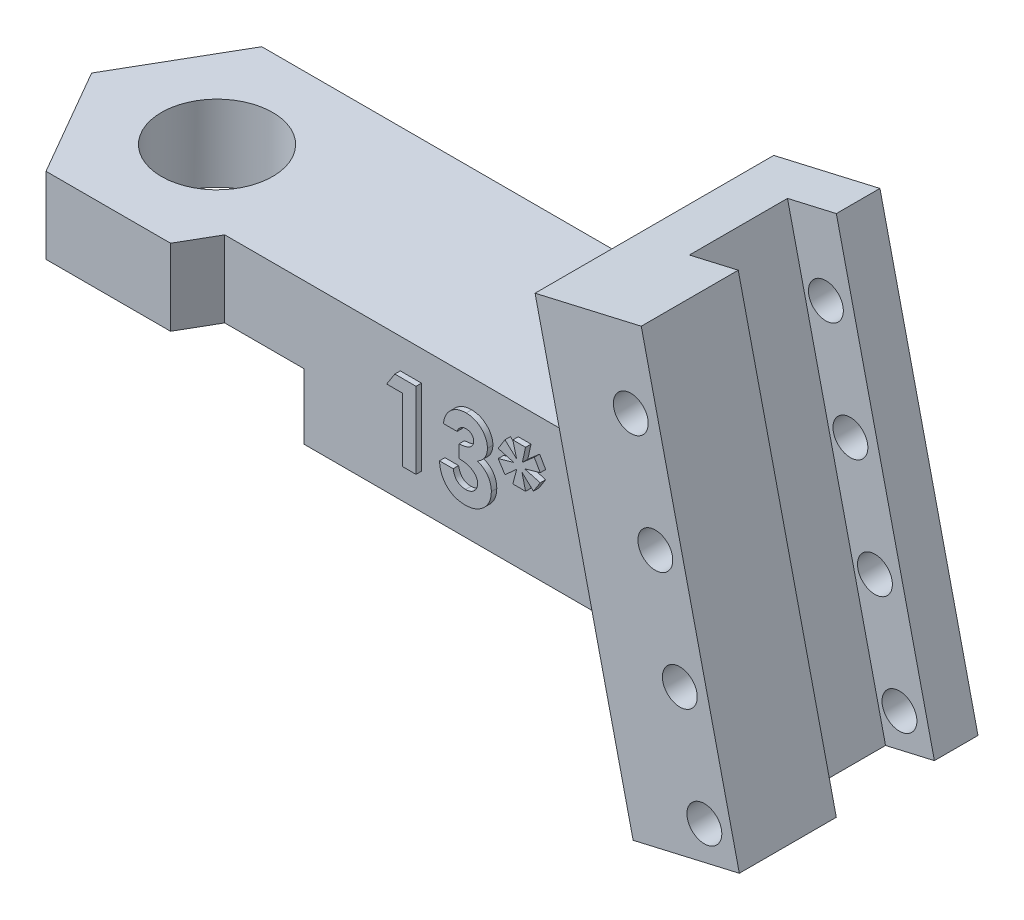
SolidWorks part; units mm, degrees
ref_plane "Front Plane" through (0, 0, 0) normal (0, 0, 1) x (1, 0, 0)
ref_plane "Top Plane" through (0, 0, 0) normal (0, 1, 0) x (1, 0, 0)
ref_plane "Right Plane" through (0, 0, 0) normal (1, 0, 0) x (0, 0, -1)
sketch "Sketch1" plane through (0, 0, 0) normal (0, 1, 0) x (1, 0, 0)
  line L1 (0, 0) -> (25, 0)
  line L2 (0, 0) -> (0, -6.75)
  line L3 (0, -6.75) -> (25, -6.75)
  line L4 (25, 0) -> (25, -6.75)
  dimension "D1" = 6.75
  dimension "D2" = 25
extrude "Boss-Extrude1" add sketch "Sketch1" along normal blind 6.5
ref_plane "Plane1" through (0, 0, 3.375) normal (0, 0, 1) x (1, 0, 0)
sketch "Sketch5" plane through (0, 6.5, 0) normal (0, 1, 0) x (1, 0, 0)
  line L0 (0, 0) -> (0, -6.75) construction
  line L1 (-5.7158, -3.375) -> (-2.8579, -8.325)
  line L2 (-2.8579, -8.325) -> (2.8579, -8.325)
  line L3 (2.8579, -8.325) -> (5.7158, -3.375)
  line L4 (5.7158, -3.375) -> (2.8579, 1.575)
  line L5 (2.8579, 1.575) -> (-2.8579, 1.575)
  line L6 (-2.8579, 1.575) -> (-5.7158, -3.375)
  circle A0 centre (0, -3.375) radius 4.95 construction
  dimension "D1" = 4.95
extrude "Boss-Extrude4" add sketch "Sketch5" against normal up to surface (6.5 mm away) up to face at (12.5, 0, 3.375)
sketch "Sketch3" plane through (0, 0, 3.375) normal (0, 0, 1) x (1, 0, 0)
  line L0 (20.6291, 13.925) -> (25.501, 15.0498)
  line L1 (25.501, 15.0498) -> (30, -4.4376)
  line L2 (30, -4.4376) -> (25.1281, -5.5624)
  line L3 (25.1281, -5.5624) -> (20.6291, 13.925)
  line L4 (3.7672, 6.5) -> (25, 6.5) construction
  point P6 (27.5641, -5)
  dimension "D1" = 30
  dimension "D2" = 5
  dimension "D3" = 20
  dimension "D4" = 77
  dimension "D6" = 5
extrude "Boss-Extrude3" add sketch "Sketch3" against normal up to surface (4.95 mm away) and the other way blind 6 up to face at (0, 3.25, -1.575)
sketch "Sketch4" plane through (-2.0083, 8.6988, 0) normal (-0.225, 0.9744, 0) x (0.9744, 0.225, 0)
  line L0 (28.2329, -9.375) -> (28.2329, 1.575) construction
  line L1 (25.9329, -0.425) -> (28.2329, -0.425)
  line L2 (25.9329, -0.425) -> (25.9329, -4.925)
  line L3 (25.9329, -4.925) -> (28.2329, -4.925)
  line L4 (28.2329, -0.425) -> (28.2329, -4.925)
  line L6 (28.2329, 1.575) -> (23.2329, 1.575) construction
  dimension "D1" = 4.5
  dimension "D2" = 2.3
  dimension "D3" = 2
extrude "Cut-Extrude1" cut sketch "Sketch4" against normal blind 23 contours L2 L3 L4 L1
sketch "Sketch6" plane through (0, 6.5, 0) normal (0, 1, 0) x (1, 0, 0)
  circle A0 centre (0, -3.3356) radius 2.55
  dimension "D1" = 5.1
extrude "Cut-Extrude2" cut sketch "Sketch6" against normal blind 10
sketch "Sketch7" plane through (0, 0, -1.575) normal (0, 0, -1) x (-1, 0, 0)
  line L0 (-2.8579, 0) -> (-23.844, 0)
  line L1 (-23.844, 0) -> (-25.1281, -5.5624)
  line L2 (-25.1281, -5.5624) -> (-30, -4.4376)
  line L3 (-30, -4.4376) -> (-25.501, 15.0498)
  line L4 (-25.501, 15.0498) -> (-20.6291, 13.925)
  line L5 (-20.6291, 13.925) -> (-22.3433, 6.5)
  line L6 (-22.3433, 6.5) -> (-2.8579, 6.5)
  line L7 (-2.8579, 6.5) -> (-2.8579, 0)
  dimension "D1" = 20
extrude "Boss-Extrude5" add sketch "Sketch7" against normal up to surface (1.575 mm away) up to face at (13.4304, 3.25, 0)
sketch "Sketch8" plane through (0, 0, 0) normal (0, -1, 0) x (-1, 0, 0)
  line L1 (-4.6765, -11.475) -> (4.6765, -11.475)
  line L2 (4.6765, -11.475) -> (9.3531, -3.375)
  line L3 (9.3531, -3.375) -> (4.6765, 4.725)
  line L4 (4.6765, 4.725) -> (-4.6765, 4.725)
  line L5 (-4.6765, 4.725) -> (-9.3531, -3.375)
  line L6 (-9.3531, -3.375) -> (-4.6765, -11.475)
  circle A0 centre (0, -3.375) radius 8.1 construction
  dimension "D1" = 16.2
extrude "Cut-Extrude3" cut sketch "Sketch8" against normal blind 3
sketch "Sketch9" plane through (0, 0, -1.575) normal (0, 0, -1) x (-1, 0, 0)
  line L0 (-30, -4.4376) -> (-25.501, 15.0498) construction
  line L1 (-25.1281, -5.5624) -> (-30, -4.4376) construction
  line L2 (-28.3959, -3.2685) -> (-25.0216, 11.347) construction
  line L3 (-30, -4.4376) -> (-25.501, 15.0498) construction
  circle A0 centre (-28.3959, -3.2685) radius 0.8
  circle A4 centre (-27.2711, 1.6033) radius 0.8
  circle A5 centre (-26.1464, 6.4752) radius 0.8
  circle A6 centre (-25.0216, 11.347) radius 0.8
  point P6 (0, 0)
  point P7 (0, 0)
  point P14 (0, 0)
  point P15 (-25.5861, 11.3628)
  dimension "D1" = 1.6
  dimension "D2" = 1.3
  dimension "D5" = 5
  dimension "D3" = 1.5
  dimension "D4" = 5
  dimension "D6" = 5
extrude "Cut-Extrude4" cut sketch "Sketch9" against normal up to surface (10.95 mm away) up to face at (25.3146, 4.7437, 9.375)
sketch "Sketch10" plane through (0, 0, 6.75) normal (0, 0, 1) x (1, 0, 0)
  text T0 "<b>13*</b>"
extrude "Boss-Extrude6" add sketch "Sketch10" along normal blind 0.25
